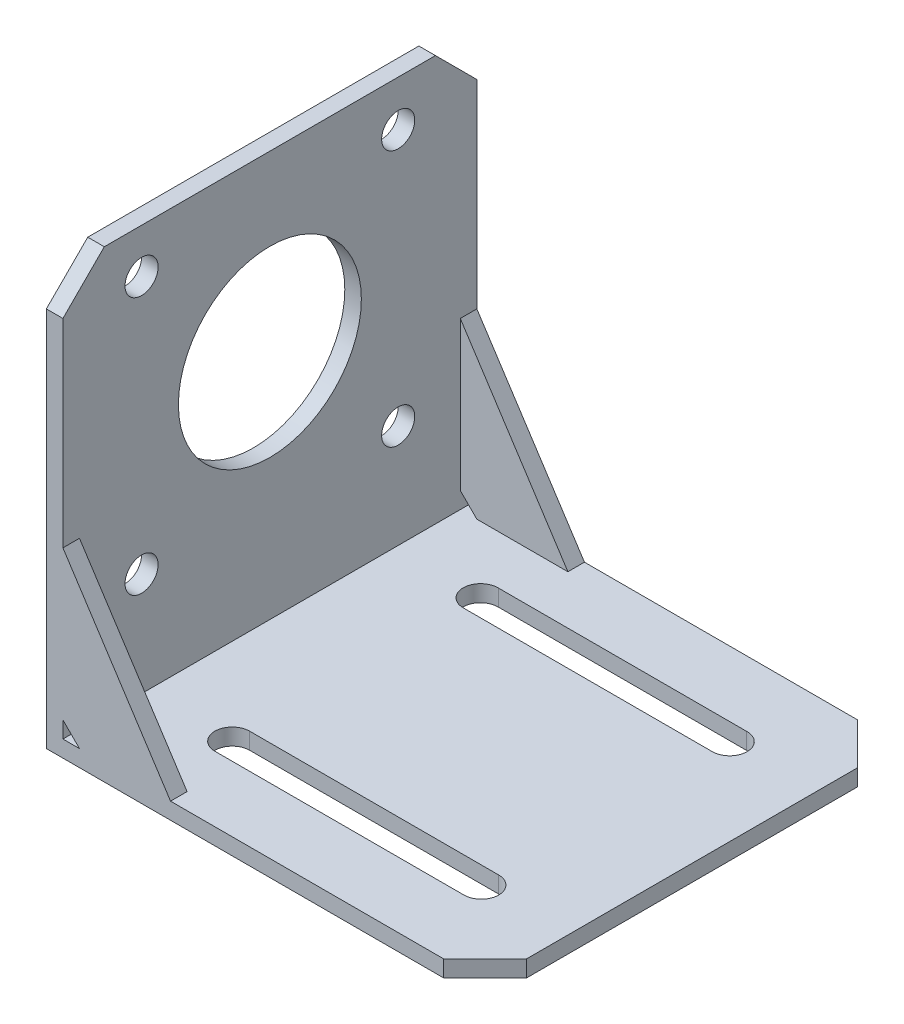
SolidWorks part; units mm, degrees
ref_plane "Front" through (0, 0, 0) normal (0, 0, 1) x (1, 0, 0)
ref_plane "Top" through (0, 0, 0) normal (0, 1, 0) x (1, 0, 0)
ref_plane "Right" through (0, 0, 0) normal (1, 0, 0) x (0, 0, -1)
sketch "Sketch1" plane through (0, 0, 0) normal (0, 0, 1) x (1, 0, 0)
  line L0 (0, 0) -> (0, 51)
  line L1 (0, 51) -> (2, 51)
  line L2 (2, 51) -> (2, 2)
  line L3 (2, 2) -> (53, 2)
  line L4 (53, 2) -> (53, 0)
  line L5 (53, 0) -> (0, 0)
  dimension "D1" = 51
  dimension "D2" = 53
  dimension "D3" = 2
  dimension "D4" = 2
extrude "Boss-Extrude1" add sketch "Sketch1" along normal blind 50
sketch "Sketch2" plane through (2, 0, 0) normal (1, 0, 0) x (0, 0, -1)
  line L0 (-25, 51) -> (-25, 2) construction
  line L1 (-50, 51) -> (0, 51) construction
  line L2 (-50, 2) -> (0, 2) construction
  line L3 (-50, 30) -> (0, 30) construction
  line L4 (-50, 2) -> (-50, 51) construction
  line L5 (0, 2) -> (0, 51) construction
  line L6 (-40.5, 51) -> (-40.5, 2) construction
  line L7 (-9.5, 51) -> (-9.5, 2) construction
  line L8 (-50, 14.5) -> (0, 14.5) construction
  line L9 (-50, 45.5) -> (0, 45.5) construction
  circle A0 centre (-25, 30) radius 11.05
  circle A1 centre (-40.5, 45.6404) radius 2
  circle A2 centre (-9.5, 45.5) radius 2
  circle A3 centre (-40.5, 14.5) radius 2
  circle A4 centre (-9.5, 14.5) radius 2
  dimension "D6" = 4
  dimension "D7" = 4
  dimension "D8" = 4
  dimension "D9" = 4
  dimension "D10" = 22.1
  dimension "D1" = 21
  dimension "D2" = 15.5
  dimension "D3" = 15.5
  dimension "D4" = 15.5
  dimension "D5" = 15.5
extrude "Cut-Extrude1" cut sketch "Sketch2" against normal through all
sketch "Sketch3" plane through (0, 2, 0) normal (0, 1, 0) x (1, 0, 0)
  line L0 (2, -25) -> (53, -25) construction
  line L1 (2, -50) -> (2, 0) construction
  line L2 (53, -50) -> (53, 0) construction
  line L3 (2, -40) -> (53, -40) construction
  line L4 (53, -50) -> (2, -50) construction
  line L5 (27.5, -50) -> (27.5, 0) construction
  line L6 (53, 0) -> (2, 0) construction
  line L7 (2, -10) -> (53, -10) construction
  line L9 (12.4553, -12.1) -> (42.5447, -12.1)
  line L11 (12.5, -7.9005) -> (42.5, -7.9005)
  line L13 (27.5, -7.9005) -> (27.5, -12.1) construction
  line L14 (12.4553, -10) -> (42.5447, -10) construction
  line L15 (12.5, -42.0995) -> (42.5, -42.0995)
  line L17 (12.4553, -37.9) -> (42.5447, -37.9)
  line L19 (27.5, -37.9) -> (27.5, -42.0995) construction
  line L20 (12.4553, -40) -> (42.5447, -40) construction
  arc A0 (42.5, -7.9005) -> (42.5447, -12.1) centre (42.5447, -10) cw
  arc A1 (12.4553, -12.1) -> (12.5, -7.9005) centre (12.4553, -10) cw
  arc A2 (12.5, -42.0995) -> (12.4553, -37.9) centre (12.4553, -40) cw
  arc A3 (42.5447, -37.9) -> (42.5, -42.0995) centre (42.5447, -40) cw
  point P16 (27.5, -10)
  point P20 (27.5, -40)
  dimension "D3" = 2.1
  dimension "D4" = 2.1
  dimension "D5" = 30
  dimension "D6" = 30
  dimension "D7" = 10.4553
  dimension "D8" = 10.4553
  dimension "D1" = 15
  dimension "D2" = 15
extrude "Cut-Extrude2" cut sketch "Sketch3" against normal blind 50
sketch "Sketch5" plane through (0, 0, 50) normal (0, 0, 1) x (1, 0, 0)
  line L0 (2, 22) -> (2, 4)
  line L1 (2, 2) -> (2, 51) construction
  line L2 (2, 4) -> (4, 2)
  line L3 (53, 2) -> (2, 2) construction
  line L4 (4, 2) -> (15, 2)
  line L5 (15, 2) -> (2, 22)
  dimension "D1" = 2
  dimension "D2" = 2
  dimension "D3" = 20
  dimension "D4" = 13
extrude "Boss-Extrude2" add sketch "Sketch5" against normal blind 2
sketch "Sketch6" plane through (0, 0, 0) normal (0, 0, -1) x (-1, 0, 0)
  line L0 (-4, 2) -> (-2, 4)
  line L1 (-2, 2) -> (-53, 2) construction
  line L2 (-2, 51) -> (-2, 2) construction
  line L3 (-2, 4) -> (-2, 22)
  line L4 (-2, 22) -> (-15, 2)
  line L5 (-15, 2) -> (-4, 2)
  dimension "D1" = 2
  dimension "D2" = 20
  dimension "D3" = 2
  dimension "D4" = 13
extrude "Boss-Extrude3" add sketch "Sketch6" against normal blind 2
chamfer "Chamfer1" distance 5 angle 45 4 edges at (53, 1, 50) (53, 1, 0) (1, 51, 50) (1, 51, 0)
